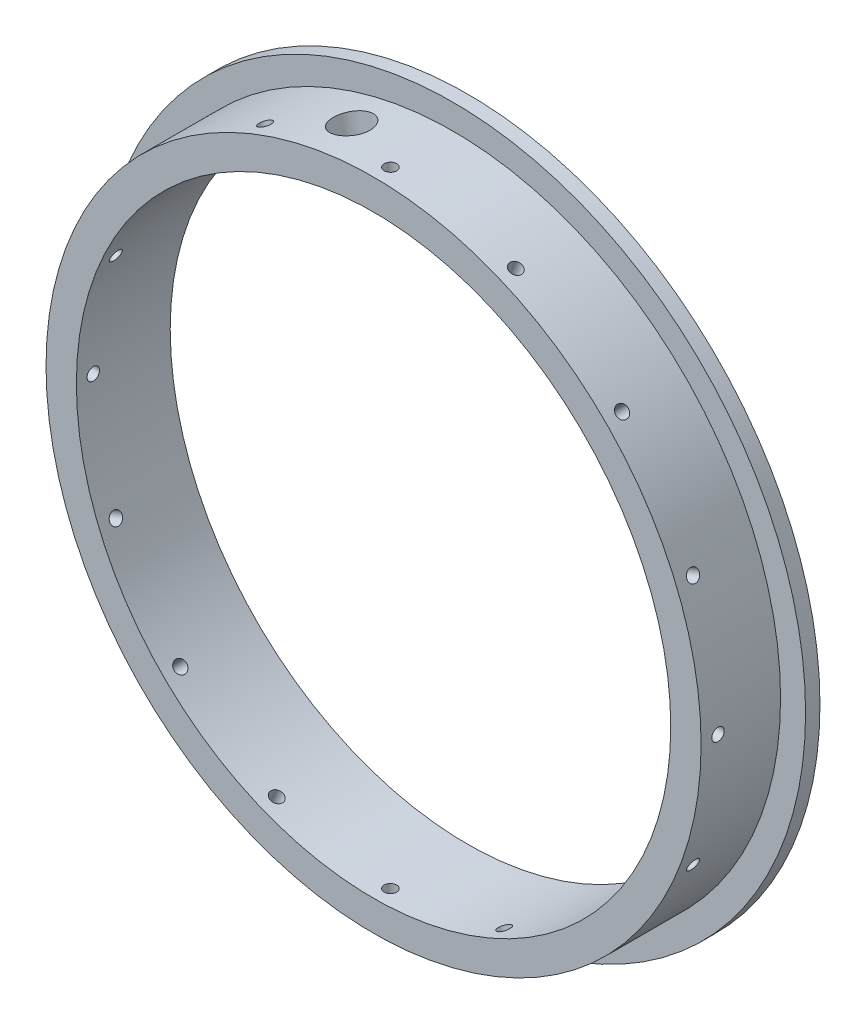
SolidWorks part; units mm, degrees
material "6061-T6 (SS)"
ref_plane "Front Plane" through (0, 0, 0) normal (0, 0, 1) x (1, 0, 0)
ref_plane "Top Plane" through (0, 0, 0) normal (0, 1, 0) x (1, 0, 0)
ref_plane "Right Plane" through (0, 0, 0) normal (1, 0, 0) x (0, 0, -1)
sketch "Sketch1" plane through (0, 0, 0) normal (0, 0, 1) x (1, 0, 0)
  circle A0 centre (0, 0) radius 71.5645
extrude "Extrude1" add sketch "Sketch1" along normal blind 19.05
sketch "Sketch2" plane through (0, 0, 19.05) normal (0, 0, 1) x (1, 0, 0)
  circle A0 centre (0, 0) radius 60.325
  dimension "D1" = 120.65
extrude "Extrude2" cut sketch "Sketch2" against normal blind 19.05
sketch "Sketch3" plane through (0, 0, 19.05) normal (0, 0, 1) x (1, 0, 0)
  circle A0 centre (0, 0) radius 66.4845
  dimension "D1" = 132.969
extrude "Extrude3" cut sketch "Sketch3" against normal blind 16.129 flip side to cut
ref_plane "Plane2" through (0, 0, 15.621) normal (0, 0, 1) x (1, 0, 0)
sketch "Sketch10" plane through (0, 0, 15.621) normal (0, 0, 1) x (1, 0, 0)
  line L0 (0, 0) -> (0, 66.4845) construction
  line L1 (0, 0) -> (66.4845, 0) construction
  circle A0 centre (0, 0) radius 66.4845 construction
sketch "Sketch13" plane through (0, 0, 15.621) normal (0, 0, 1) x (1, 0, 0)
  arc A0 (0, 66.4845) -> (25.4425, 61.4237) centre (0, 0) cw
sketch "Sketch14" plane through (0, 0, 15.621) normal (0, 0, 1) x (1, 0, 0)
  line L1 (0, 0) -> (25.4425, 61.4237) construction
  arc A0 (25.4425, 61.4237) -> (47.0116, 47.0116) centre (0, 0) cw
sketch "Sketch15" plane through (0, 0, 15.621) normal (0, 0, 1) x (1, 0, 0)
  line L1 (0, 0) -> (47.0116, 47.0116) construction
  arc A0 (47.0116, 47.0116) -> (61.4237, 25.4425) centre (0, 0) cw
ref_plane "Plane3" through (25.4425, 61.4237, 15.621) normal (0.3827, 0.9239, 0) x (-0.9239, 0.3827, 0)
ref_plane "Plane5" through (47.0116, 47.0116, 15.621) normal (0.7071, 0.7071, 0) x (-0.7071, 0.7071, 0)
sketch "Sketch39" plane through (0, 0, 15.621) normal (0, 0, 1) x (1, 0, 0)
  line L1 (0, 0) -> (61.4237, 25.4425) construction
ref_plane "Plane6" through (61.4237, 25.4425, 15.621) normal (0.9239, 0.3827, 0) x (0, 0, -1)
hole_wizard "#39 (0.0995) Diameter Hole5" positions "Sketch42" profile "Sketch41" hole size "#39" standard "Ansi Inch"
sketch "Sketch42" plane through (61.4237, 25.4425, 15.621) normal (0.9239, 0.3827, 0) x (0, 0, -1)
  point P1 (0, 0)
sketch "Sketch41" plane through (61.4237, 25.4425, 15.621) normal (0, 0, 1) x (-0.3827, 0.9239, 0)
  line L0 (0, 0) -> (0, 13.4593)
  line L1 (0, 13.4593) -> (1.2636, 12.7)
  line L2 (1.2636, 12.7) -> (1.2636, 0)
  line L5 (1.2636, 0) -> (0, 0)
  line L10 (0, 13.4593) -> (-1.2636, 12.7) construction
  line L11 (0, -6.35) -> (0, 107.95) construction
  dimension "Hole Dia." = 2.5273
  dimension "Hole Depth" = 12.7
  dimension "Drill Angle" = 118
pattern_circular "CirPattern1" count 16 over 360 about axis through (0, 0, 0) along (0, 0, 1) of "#39 (0.0995) Diameter Hole5"
sketch "Sketch54" plane through (0, 0, 15.621) normal (0, 0, 1) x (1, 0, 0)
  line L0 (0, 0) -> (61.4237, -25.4425) construction
  arc A0 (66.4845, 0) -> (61.4237, -25.4425) centre (0, 0) cw
sketch "Sketch56" plane through (0, 0, 15.621) normal (0, 0, 1) x (1, 0, 0)
  line L0 (0, 0) -> (47.0116, -47.0116) construction
  arc A0 (61.4237, -25.4425) -> (47.0116, -47.0116) centre (0, 0) cw
sketch "Sketch58" plane through (0, 0, 15.621) normal (0, 0, 1) x (1, 0, 0)
  line L0 (0, 0) -> (25.4425, -61.4237) construction
  arc A0 (47.0116, -47.0116) -> (25.4425, -61.4237) centre (0, 0) cw
ref_plane "Plane22" through (0, 0, 10.541) normal (0, 0, 1) x (1, 0, 0)
sketch "Sketch100" plane through (0, 0, 10.541) normal (0, 0, 1) x (1, 0, 0)
  line L0 (0, 0) -> (0, 66.4845) construction
  circle A0 centre (0, 0) radius 66.4845 construction
  arc A1 (0, 66.4845) -> (-12.9705, 65.207) centre (0, 0) ccw
sketch "Sketch101" plane through (0, 0, 10.541) normal (0, 0, 1) x (1, 0, 0)
  line L0 (0, 0) -> (-12.9705, 65.207) construction
ref_plane "Plane23" through (-12.9705, 65.207, 10.541) normal (-0.1951, 0.9808, 0) x (-0.9808, -0.1951, 0)
sketch "Sketch102" plane through (-12.9705, 65.207, 10.541) normal (-0.1951, 0.9808, 0) x (-0.9808, -0.1951, 0)
  circle A0 centre (0, 0) radius 3.81
  dimension "D1" = 7.62
extrude "Extrude6" cut sketch "Sketch102" against normal blind 10.16
